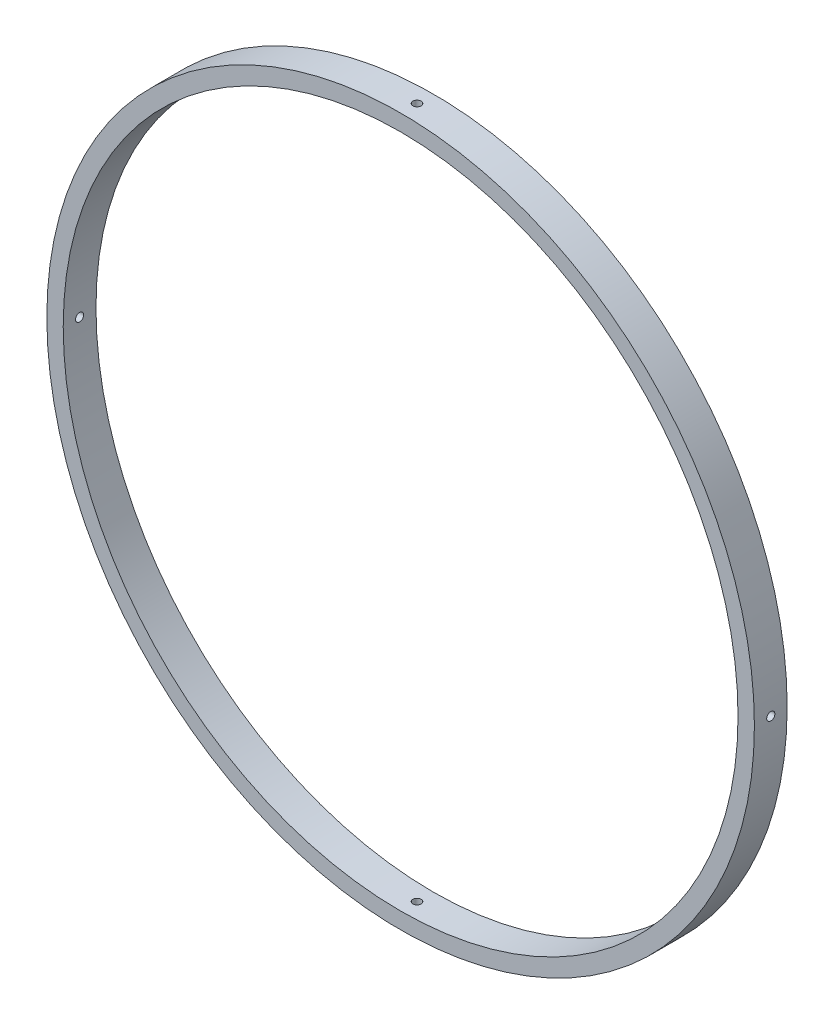
SolidWorks part; units mm, degrees
ref_plane "Front Plane" through (0, 0, 0) normal (0, 0, 1) x (1, 0, 0)
ref_plane "Top Plane" through (0, 0, 0) normal (0, 1, 0) x (1, 0, 0)
ref_plane "Right Plane" through (0, 0, 0) normal (1, 0, 0) x (0, 0, -1)
sketch "Sketch3" plane through (0, 0, 0) normal (0, 0, 1) x (1, 0, 0)
  circle A0 centre (0, 0) radius 65.405
  circle A1 centre (0, 0) radius 68.58
  dimension "D1" = 130.81
  dimension "D2" = 3.175
extrude "Boss-Extrude1" add sketch "Sketch3" along normal mid plane 6.35
sketch "Sketch4" plane through (0, 0, 0) normal (0, 1, 0) x (1, 0, 0)
  circle A0 centre (0, 0) radius 0.7937
  dimension "D1" = 1.5875
extrude "Cut-Extrude1" cut sketch "Sketch4" against normal through all
pattern_circular "CirPattern1" count 4 over 360 about axis through (0, 0, 3.175) along (0, 0, -1) of "Cut-Extrude1"
equation "\"AIRFRAME_OD\"= 5.15in"
equation "\"AIRFRAME_ID\"= 4.99in"
equation "\"FLAT_T\"= 0.125in"
equation "\"NOSE_EXP_L\"= 27in"
equation "\"NOSE_SHOULDER_L\"= 5in"
equation "\"MAIN_L\"= 30in"
equation "\"RECO_COUP_L\"= 10in"
equation "\"RECO_SWITCH_L\"= 2in"
equation "\"DROGUE_L\"= 20in"
equation "\"ATS_FORE_COUP_L\"= 5.5in"
equation "\"ATS_AFT_COUP_L\"= 4.5in"
equation "\"LOWER_L\"= 30in"
equation "\"FIN_N\"= 4"
equation "\"CR_AFT_X\"= 0.5in"
equation "\"CR_FORE_X\"= 9.25in"
equation "\"COUPLER_OD\"= 4.998in"
equation "\"COUPLER_ID\"= 4.85in"
equation "\"RECO_ROD_X\"= 3.5in"
equation "\"ATS_ROD_X\"= 3.75in"
equation "\"FIN_ROOT\"= 8in"
equation "\"FIN_X\"= 0.75in"
equation "\"MOTOR_OD\"= 3.091in"
equation "\"MOTOR_ID\"= 3.00in"
equation "\"MOTOR_L\"= 14in"
equation "\"MOTOR_LOWER_X\"= 2in"
equation "\"D1@Sketch3\"=\"AIRFRAME_OD\""
